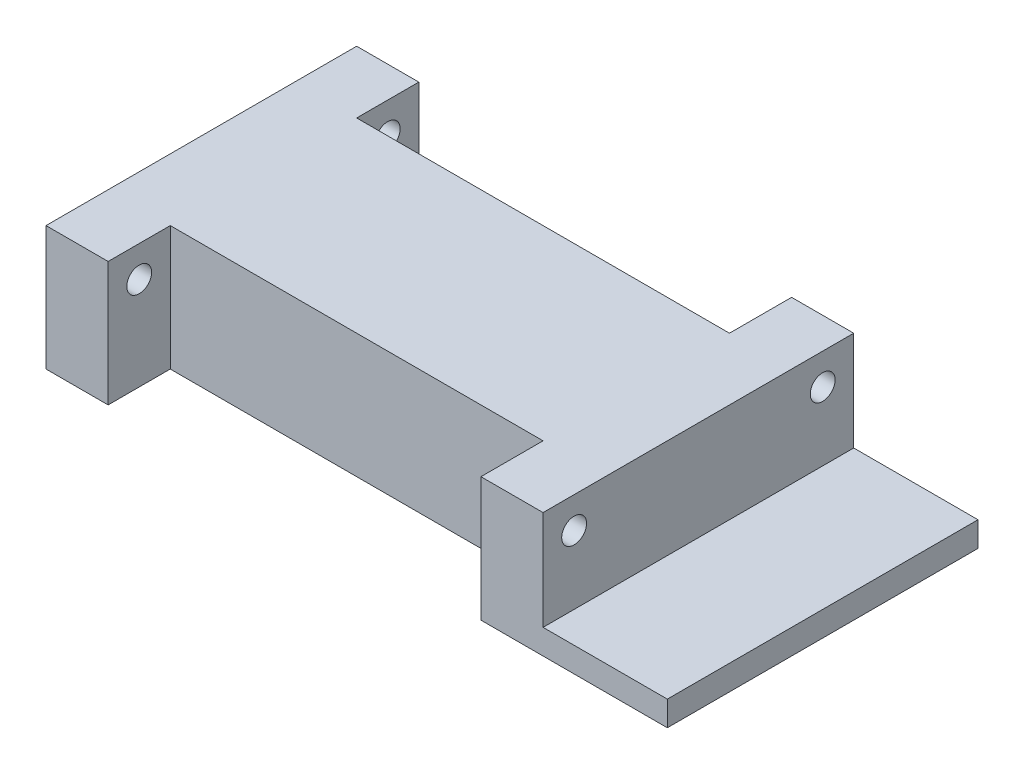
SolidWorks part; units mm, degrees
material "Cast Stainless Steel"
ref_plane "Front Plane" through (0, 0, 0) normal (0, 0, 1) x (1, 0, 0)
ref_plane "Top Plane" through (0, 0, 0) normal (0, 1, 0) x (1, 0, 0)
ref_plane "Right Plane" through (0, 0, 0) normal (1, 0, 0) x (0, 0, -1)
sketch "Sketch2" plane through (0, 0, 0) normal (0, 1, 0) x (1, 0, 0)
  line L1 (0, 0) -> (400, 0)
  line L2 (0, 0) -> (0, 150)
  line L3 (0, 150) -> (400, 150)
  line L4 (400, 0) -> (400, 150)
  dimension "D1" = 150
  dimension "D2" = 400
extrude "Boss-Extrude1" add sketch "Sketch2" along normal blind 50
sketch "Sketch3" plane through (400, 0, 0) normal (1, 0, 0) x (0, 0, -1)
  line L1 (0, 0) -> (-50, 0)
  line L2 (0, 0) -> (0, 50)
  line L3 (0, 50) -> (-50, 50)
  line L4 (-50, 0) -> (-50, 50)
  line L5 (150, 0) -> (200, 0)
  line L6 (150, 0) -> (150, 50)
  line L7 (150, 50) -> (200, 50)
  line L8 (200, 0) -> (200, 50)
  dimension "D1" = 50
  dimension "D2" = 50
extrude "Boss-Extrude2" add sketch "Sketch3" against normal blind 50
ref_plane "Plane1" through (200, 0, 0) normal (1, 0, 0) x (0, 0, -1)
mirror "Mirror4" about plane through (200, 0, 0) normal (1, 0, 0) of "Boss-Extrude2"
sketch "Sketch4" plane through (400, 0, 0) normal (1, 0, 0) x (0, 0, -1)
  line L0 (-50, 50) -> (-50, 0) construction
  line L1 (200, 0) -> (200, 50) construction
  circle A0 centre (-25, 25) radius 10
  circle A1 centre (175, 25) radius 10
  point P8 (200, 25)
  dimension "D2" = 20
  dimension "D3" = 20
  dimension "D1" = 25
  dimension "D4" = 25
extrude "Cut-Extrude1" cut sketch "Sketch4" against normal blind 444
sketch "Sketch6" plane through (0, 0, 0) normal (0, -1, 0) x (1, 0, 0)
  line L0 (0, 50) -> (0, -200)
  line L1 (0, -200) -> (50, -200)
  line L2 (50, -200) -> (50, -150)
  line L3 (50, -150) -> (350, -150)
  line L4 (350, -150) -> (350, -200)
  line L5 (350, -200) -> (400, -200)
  line L6 (400, -200) -> (400, 50)
  line L7 (400, 50) -> (350, 50)
  line L8 (350, 50) -> (350, 0)
  line L9 (350, 0) -> (50, 0)
  line L10 (50, 0) -> (50, 50)
  line L11 (50, 50) -> (0, 50)
extrude "Boss-Extrude3" add sketch "Sketch6" along normal blind 50
sketch "Sketch7" plane through (400, 0, 0) normal (1, 0, 0) x (0, 0, -1)
  line L0 (200, -50) -> (200, 50) construction
  line L1 (-50, -50) -> (200, -50)
  line L2 (-50, -50) -> (-50, -30)
  line L3 (-50, -30) -> (200, -30)
  line L4 (200, -50) -> (200, -30)
  point P7 (200, -50)
  dimension "D1" = 20
extrude "Boss-Extrude4" add sketch "Sketch7" along normal blind 100
